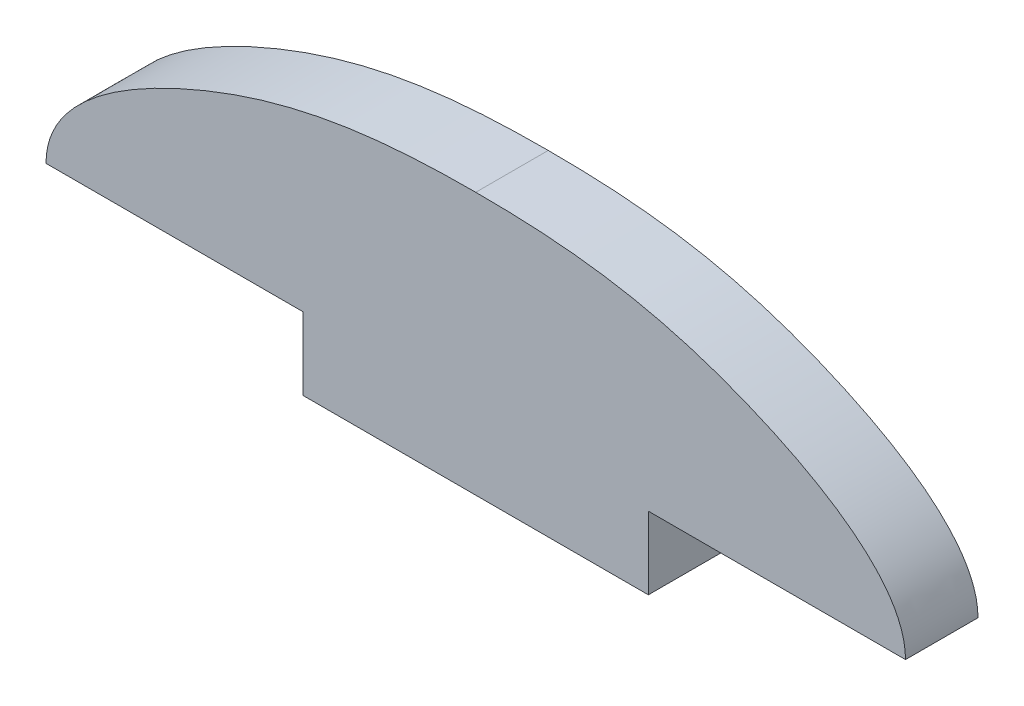
SolidWorks part; units mm, degrees
ref_plane "Front" through (0, 0, 0) normal (0, 0, 1) x (1, 0, 0)
ref_plane "Top" through (0, 0, 0) normal (0, 1, 0) x (1, 0, 0)
ref_plane "Right" through (0, 0, 0) normal (1, 0, 0) x (0, 0, -1)
sketch "Sketch1" plane through (0, 0, 0) normal (0, 0, 1) x (1, 0, 0)
  line L0 (-31.623, 41.4528) -> (31.623, 41.4528)
  line L1 (0, 41.4528) -> (0, 55.4228) construction
  line L4 (12.7, 36.1188) -> (12.7, 41.4528)
  line L5 (12.7, 41.4528) -> (-12.7, 41.4528)
  line L6 (-12.7, 41.4528) -> (-12.7, 36.1188)
  line L7 (-12.7, 36.1188) -> (12.7, 36.1188)
  line L8 (12.7, 36.1188) -> (12.7, 41.4528)
  line L9 (12.7, 41.4528) -> (-12.7, 41.4528)
  line L10 (-12.7, 41.4528) -> (-12.7, 36.1188)
  line L11 (-12.7, 36.1188) -> (12.7, 36.1188)
  spline S0 degree 3 poles (-31.623, 41.4528) (-31.623, 45.8774) (-17.945, 54.272) (-6.9903, 55.4228) (0, 55.4228) knots 0 0 0 0 0.410118 1 1 1 1
  spline S1 degree 3 poles (31.623, 41.4528) (31.623, 45.8774) (17.945, 54.272) (6.9903, 55.4228) (0, 55.4228) knots 0 0 0 0 0.410118 1 1 1 1
  point P11 (-24.8096, 50.0526)
  point P12 (-20.8619, 51.5446)
  dimension "D2" = 13.97
  dimension "D1" = 0
extrude "Boss-Extrude1" add sketch "Sketch1" along normal blind 5.334 contours L0 L1 S0 | L1 L9 L0 S1 | L10 L11 L8 L9 L0
